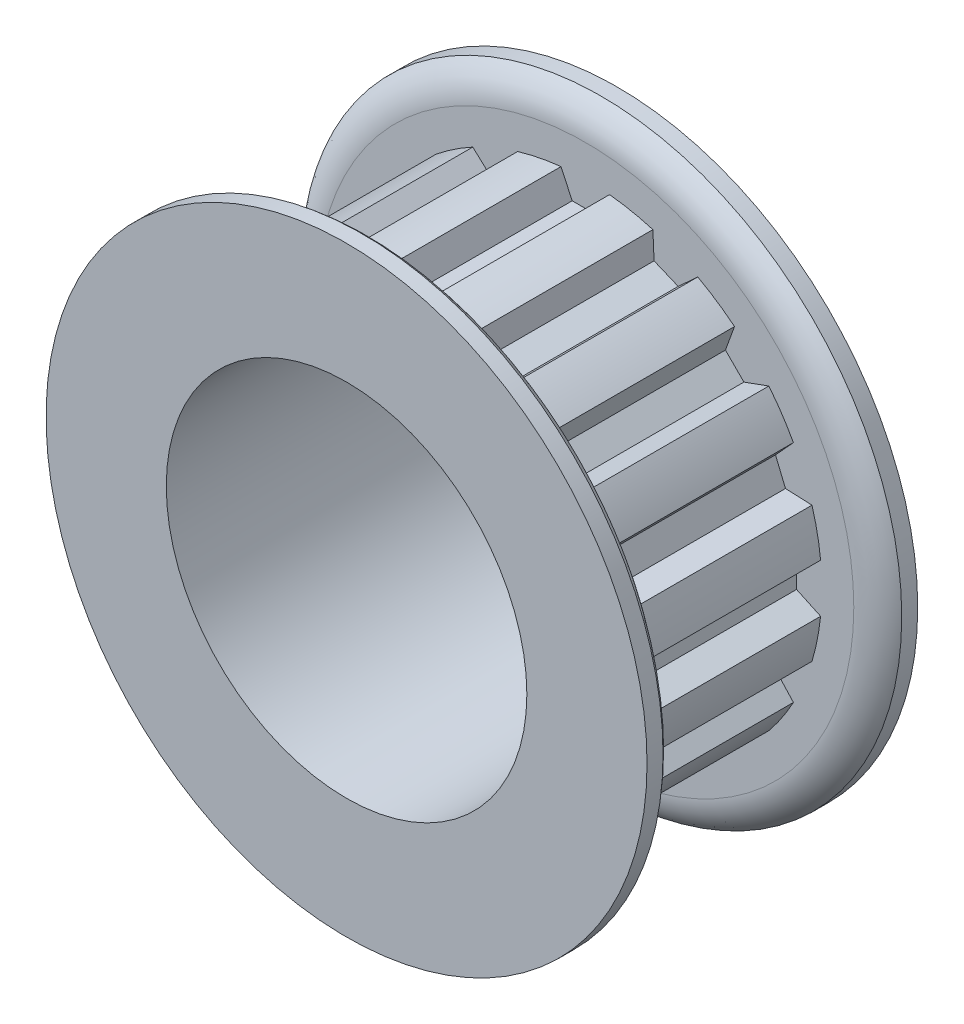
SolidWorks part; units mm, degrees
ref_plane "Front Plane" through (0, 0, 0) normal (0, 0, 1) x (1, 0, 0)
ref_plane "Top Plane" through (0, 0, 0) normal (0, 1, 0) x (1, 0, 0)
ref_plane "Right Plane" through (0, 0, 0) normal (1, 0, 0) x (0, 0, -1)
sketch "Sketch1" plane through (0, 0, 0) normal (0, 0, 1) x (1, 0, 0)
  line L0 (-1.2827, 12.4333) -> (-0.6905, 11.1633)
  line L1 (-0.6905, 11.1633) -> (0.6905, 11.1633)
  line L2 (0.6905, 11.1633) -> (1.2827, 12.4333)
  line L3 (-1.2827, 12.4333) -> (1.2827, 12.4333)
  line L4 (0, 0) -> (0, 11.1633) construction
  line L5 (0, 11.1633) -> (0, 13.4493) construction
  circle A0 centre (0, 0) radius 12.9413 construction
  circle A1 centre (0, 0) radius 15.875 construction
  circle A2 centre (0, 0) radius 12.4993 construction
  point P6 (0, 12.4333)
  point P11 (0, 12.9413)
  point P13 (0, 15.875)
  point P14 (0, 12.4993)
  dimension "D1" = 1.016
  dimension "PD" = 25.8826
  dimension "D2" = 0.508
  dimension "OD" = 31.75
  dimension "b" = 50
  dimension "bt" = 2.5654
  dimension "ht" = 1.27
  dimension "hs" = 2.286
sketch "Sketch2" plane through (0, 0, 0) normal (1, 0, 0) x (0, 0, -1)
  line L0 (-3.9878, 3.175) -> (10.3124, 3.175)
  line L3 (-3.9878, 8.7376) -> (-3.9878, 15.875)
  line L4 (-3.9878, 15.875) -> (-2.2987, 15.875) construction
  line L5 (-2.2987, 15.875) -> (-2.2987, 12.4993) construction
  line L6 (-2.2987, 12.4993) -> (8.6233, 12.4993)
  line L7 (8.6233, 12.4993) -> (8.6233, 15.875) construction
  line L8 (8.6233, 15.875) -> (10.3124, 15.875) construction
  line L9 (10.3124, 15.875) -> (10.3124, 3.175)
  line L10 (-10.3124, 0) -> (10.3124, 0) construction
  line L11 (-3.9878, 8.7376) -> (-3.9878, 3.175)
  line L13 (-3.9878, 15.875) -> (-3.1432, 15.875)
  line L14 (-2.2987, 14.1871) -> (-2.2987, 12.4993)
  line L15 (8.6233, 12.4993) -> (8.6233, 14.1871)
  line L16 (9.4679, 15.875) -> (10.3124, 15.875)
  arc A0 (-2.2987, 14.1871) -> (-3.1432, 15.875) centre (-4.4076, 14.1871) ccw
  arc A1 (8.6233, 14.1871) -> (9.4679, 15.875) centre (10.7322, 14.1871) cw
  point P12 (-2.2987, 14.1871)
  point P14 (-3.1432, 15.875)
  point P20 (8.6233, 14.1871)
  point P21 (9.4679, 15.875)
  point P25 (8.6233, 0)
  point P26 (-2.2987, 0)
  dimension "D1" = 5.5626
  dimension "OA" = 20.6248
  dimension "Bore" = 6.35
  dimension "Outside Width" = 14.3002
  dimension "Inside Width" = 10.922
revolve "Revolve1" add sketch "Sketch2" angle 360 mid plane about L10
sketch "Sketch3" plane through (0, 0, 0) normal (0, 0, 1) x (1, 0, 0)
  line L0 (-0.6905, 11.1633) -> (0.6905, 11.1633) construction
  line L1 (0.6905, 11.1633) -> (1.2827, 12.4333) construction
  line L2 (-1.2827, 12.4333) -> (-0.6905, 11.1633) construction
  line L3 (-0.6905, 11.1633) -> (0.6905, 11.1633)
  line L4 (0.6905, 11.1633) -> (1.2827, 12.4333)
  line L5 (-1.2827, 12.4333) -> (-0.6905, 11.1633)
  circle A0 centre (0, 0) radius 12.4993 construction
  arc A1 (1.2827, 12.4333) -> (-1.2827, 12.4333) centre (0, 0) ccw
extrude "Cut-Extrude1" cut sketch "Sketch3" against normal up to vertex (8.6233 mm away) from vertex at 2.2987 starting at point (0, 12.4993, 2.2987)
pattern_circular "CirPattern1" count 16 over 360 about axis through (0, 0, 0) along (0, 0, 1) of "Cut-Extrude1"
sketch "Sketch8" plane through (0, 0, 3.9878) normal (0, 0, 1) x (1, 0, 0)
  circle A0 centre (0, 0) radius 9.525
  dimension "D1" = 19.05
extrude "Cut-Extrude2" cut sketch "Sketch8" against normal through all
